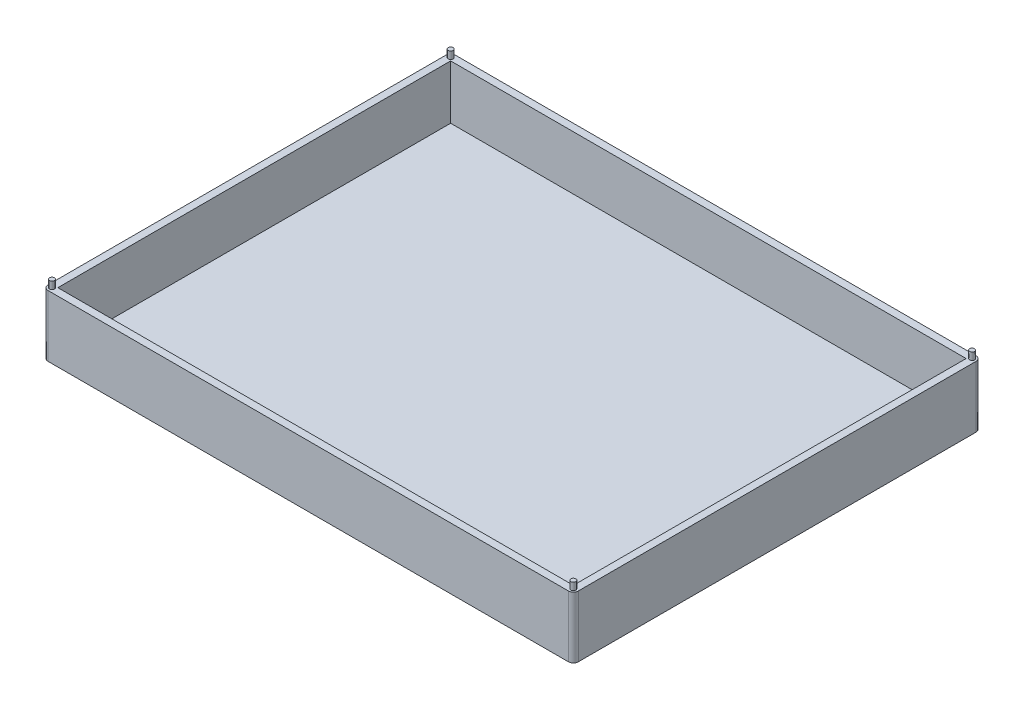
SolidWorks part; units mm, degrees
ref_plane "Plan de face" through (0, 0, 0) normal (0, 0, 1) x (1, 0, 0)
ref_plane "Plan de dessus" through (0, 0, 0) normal (0, 1, 0) x (1, 0, 0)
ref_plane "Plan de droite" through (0, 0, 0) normal (1, 0, 0) x (0, 0, -1)
sketch "Esquisse2" plane through (0, 0, 0) normal (0, 1, 0) x (1, 0, 0)
  line L2 (159.0311, 62.4882) -> (-56.9689, 62.4882)
  line L3 (159.0311, 62.4882) -> (159.0311, -103.5118)
  line L5 (-53.9689, 59.4882) -> (156.0311, 59.4882)
  line L6 (-53.9689, 59.4882) -> (-53.9689, -100.5118)
  line L7 (-53.9689, -100.5118) -> (156.0311, -100.5118)
  line L8 (156.0311, 59.4882) -> (156.0311, -100.5118)
  line L9 (159.0311, -103.5118) -> (-56.9689, -103.5118)
  line L10 (-56.9689, 62.4882) -> (-56.9689, -103.5118)
  dimension "D1" = 3
  dimension "D2" = 210
  dimension "D3" = 160
  dimension "D4" = 3
  dimension "D5" = 3
  dimension "D6" = 3
extrude "Boss.-Extru.1" add sketch "Esquisse2" along normal blind 25 contours L5 L8 L7 L6 | L3 L2 L10 L9
sketch "Esquisse4" plane through (0, 0, 0) normal (0, 1, 0) x (1, 0, 0)
  line L1 (-53.9689, -100.5118) -> (156.0311, -100.5118)
  line L2 (-53.9689, -100.5118) -> (-53.9689, 59.4882)
  line L3 (-53.9689, 59.4882) -> (156.0311, 59.4882)
  line L4 (156.0311, -100.5118) -> (156.0311, 59.4882)
extrude "Boss.-Extru.3" add sketch "Esquisse4" along normal blind 3 contours L2 L1 L4 L3
sketch "Esquisse14" plane through (0, 25, 0) normal (0, 1, 0) x (1, 0, 0)
  line L0 (159.0311, 62.4882) -> (159.0311, -103.5118) construction
  line L2 (159.0311, 62.4882) -> (-56.9689, 62.4882) construction
  circle A0 centre (157.2311, 60.6882) radius 1
  dimension "D1" = 2
  dimension "D2" = 1.8
  dimension "D3" = 1.8
fillet "Congé2" radius 2 1 edges at (159.0311, 12.5, -62.4882)
fillet "Congé3" radius 2 1 edges at (159.0311, 12.5, 103.5118)
fillet "Congé4" radius 2 1 edges at (-56.9689, 12.5, 103.5118)
fillet "Congé5" radius 2 1 edges at (-56.9689, 12.5, -62.4882)
sketch "Esquisse17" plane through (0, 25, 0) normal (0, 1, 0) x (1, 0, 0)
  line L0 (159.0311, 60.4882) -> (159.0311, -101.5118) construction
  line L1 (157.0311, -103.5118) -> (-54.9689, -103.5118) construction
  circle A0 centre (157.2311, -101.7118) radius 1
  dimension "D3" = 2
  dimension "D1" = 1.8
  dimension "D2" = 1.8
sketch "Esquisse18" plane through (0, 25, 0) normal (0, 1, 0) x (1, 0, 0)
  line L0 (157.0311, -103.5118) -> (-54.9689, -103.5118) construction
  line L1 (-56.9689, 60.4882) -> (-56.9689, -101.5118) construction
  circle A0 centre (-55.1689, -101.7118) radius 1
  dimension "D3" = 2
  dimension "D1" = 1.8
  dimension "D2" = 1.8
sketch "Esquisse19" plane through (0, 25, 0) normal (0, 1, 0) x (1, 0, 0)
  line L0 (-56.9689, 60.4882) -> (-56.9689, -101.5118) construction
  line L1 (157.0311, 62.4882) -> (-54.9689, 62.4882) construction
  circle A0 centre (-55.1689, 60.6882) radius 1
  dimension "D3" = 2
  dimension "D1" = 1.8
  dimension "D2" = 1.8
extrude "Boss.-Extru.8" add sketch "Esquisse19" along normal blind 3 contours A0
extrude "Boss.-Extru.9" add sketch "Esquisse18" along normal blind 3
extrude "Boss.-Extru.10" add sketch "Esquisse17" along normal blind 3 contours A0
extrude "Boss.-Extru.11" add sketch "Esquisse14" along normal blind 3
